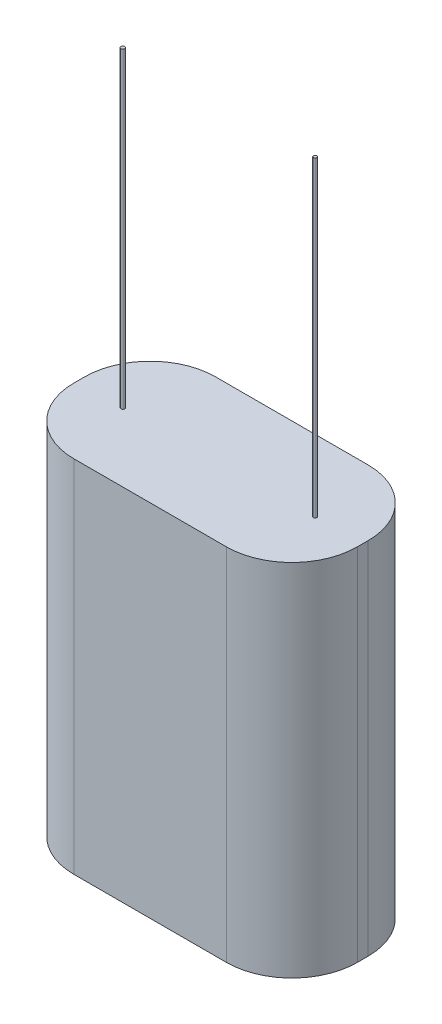
SolidWorks part; units mm, degrees
ref_plane "Front Plane" through (0, 0, 0) normal (0, 0, 1) x (1, 0, 0)
ref_plane "Top Plane" through (0, 0, 0) normal (0, 1, 0) x (1, 0, 0)
ref_plane "Right Plane" through (0, 0, 0) normal (1, 0, 0) x (0, 0, -1)
sketch "Sketch1" plane through (0, 0, 0) normal (0, 0, 1) x (1, 0, 0)
  line L1 (-13.765, -31.8927) -> (2.745, -31.8927)
  line L2 (-13.765, -31.8927) -> (-13.765, -10.9377)
  line L3 (-13.765, -10.9377) -> (2.745, -10.9377)
  line L4 (2.745, -31.8927) -> (2.745, -10.9377)
  point P0 (0, 0)
extrude "Boss-Extrude1" add sketch "Sketch1" along normal blind 8.255
fillet "Fillet1" radius 3.81 4 edges at (-13.765, -21.4152, 0) (-13.765, -21.4152, 8.255) (2.745, -21.4152, 0) (2.745, -21.4152, 8.255)
sketch "Sketch2" plane through (0, -10.9377, 0) normal (0, 1, 0) x (1, 0, 0)
  circle A0 centre (0, -4.1606) radius 0.0958
  circle A1 centre (-11.094, -4.2564) radius 0.112
extrude "Boss-Extrude2" add sketch "Sketch2" along normal blind 18.161
